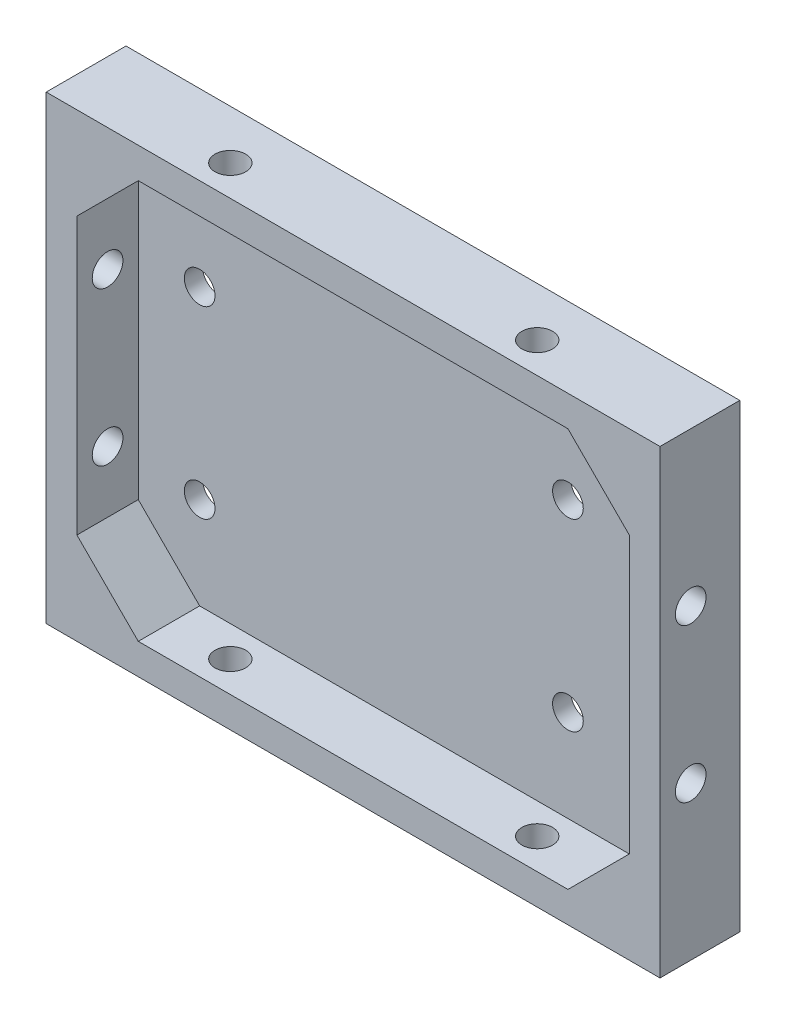
SolidWorks part; units mm, degrees
ref_plane "Plan de face" through (0, 0, 0) normal (0, 0, 1) x (1, 0, 0)
ref_plane "Plan de dessus" through (0, 0, 0) normal (0, 1, 0) x (1, 0, 0)
ref_plane "Plan de droite" through (0, 0, 0) normal (1, 0, 0) x (0, 0, -1)
sketch "Esquisse1" plane through (0, 0, 0) normal (0, 0, 1) x (1, 0, 0)
  line L0 (44.1184, 33.7284) -> (54.1184, 33.7284)
  line L1 (-45.8816, 33.7284) -> (44.1184, 33.7284)
  line L2 (-45.8816, 33.7284) -> (-45.8816, -41.2716)
  line L3 (-45.8816, -41.2716) -> (54.1184, -41.2716)
  line L4 (54.1184, 23.7284) -> (54.1184, -41.2716)
  line L5 (54.1184, 33.7284) -> (54.1184, 23.7284)
  point P6 (54.1184, 33.7284)
  dimension "D1" = 100
  dimension "D2" = 75
extrude "Boss.-Extru.1" add sketch "Esquisse1" along normal blind 13
shell "Coque1" thickness 5
sketch "Esquisse2" plane through (-45.8816, 0, 0) normal (-1, 0, 0) x (0, 0, 1)
  line L0 (13, 33.7284) -> (13, -41.2716) construction
  line L1 (13, 33.7284) -> (0, 33.7284) construction
  line L2 (13, -41.2716) -> (0, -41.2716) construction
  circle A0 centre (8, 8.7284) radius 2.5
  circle A1 centre (8, -16.2716) radius 2.5
  dimension "D1" = 5
  dimension "D2" = 5
  dimension "D3" = 5
  dimension "D4" = 5
  dimension "D5" = 25
  dimension "D6" = 25
extrude "Enlèv. mat.-Extru.1" cut sketch "Esquisse2" against normal up to surface (100 mm away) contours A1 | A0 up to face at (54.1184, -3.7716, 6.5)
sketch "Esquisse3" plane through (0, -41.2716, 0) normal (0, -1, 0) x (1, 0, 0)
  line L0 (-45.8816, 13) -> (54.1184, 13) construction
  line L2 (54.1184, 13) -> (54.1184, 0) construction
  line L3 (-45.8816, 13) -> (-45.8816, 0) construction
  circle A0 centre (-20.8816, 8) radius 2.5
  circle A1 centre (29.1184, 8) radius 2.5
  dimension "D1" = 5
  dimension "D2" = 5
  dimension "D3" = 5
  dimension "D4" = 5
  dimension "D5" = 25
  dimension "D6" = 25
extrude "Enlèv. mat.-Extru.2" cut sketch "Esquisse3" against normal up to surface (75 mm away) up to face at (4.1184, 33.7284, 6.5)
sketch "Esquisse4" plane through (0, 0, 3) normal (0, 0, 1) x (1, 0, 0)
  line L0 (-30.8816, 28.7284) -> (-40.8816, 18.7284)
  line L1 (49.1184, 28.7284) -> (-40.8816, 28.7284) construction
  line L2 (-40.8816, 28.7284) -> (-40.8816, -36.2716) construction
  line L3 (-40.8816, 18.7284) -> (-40.8816, 28.7284)
  line L4 (-40.8816, 28.7284) -> (-30.8816, 28.7284)
  line L5 (49.1184, 28.7284) -> (49.1184, 18.7284)
  line L6 (49.1184, -36.2716) -> (49.1184, 28.7284) construction
  line L7 (49.1184, 18.7284) -> (39.1184, 28.7284)
  line L8 (39.1184, 28.7284) -> (49.1184, 28.7284)
  line L9 (49.1184, 28.7284) -> (-40.8816, 28.7284) construction
  line L10 (49.1184, -36.2716) -> (49.1184, -26.2716)
  line L11 (49.1184, -26.2716) -> (39.1184, -36.2716)
  line L12 (-40.8816, -36.2716) -> (49.1184, -36.2716) construction
  line L13 (39.1184, -36.2716) -> (49.1184, -36.2716)
  line L14 (-30.8816, -36.2716) -> (-40.8816, -26.2716)
  line L15 (-40.8816, 28.7284) -> (-40.8816, -36.2716) construction
  line L16 (-40.8816, -26.2716) -> (-40.8816, -36.2716)
  line L17 (-40.8816, -36.2716) -> (-30.8816, -36.2716)
  dimension "D1" = 10
  dimension "D2" = 10
  dimension "D3" = 10
  dimension "D4" = 10
  dimension "D5" = 10
  dimension "D6" = 10
  dimension "D7" = 10
  dimension "D8" = 10
extrude "Boss.-Extru.2" add sketch "Esquisse4" along normal up to surface (10 mm away) up to face at (4.1184, -3.7716, 13)
sketch "Esquisse6" plane through (0, 0, 3) normal (0, 0, 1) x (1, 0, 0)
  line L0 (-45.8816, -41.2716) -> (54.1184, -41.2716) construction
  line L1 (54.1184, -41.2716) -> (54.1184, 33.7284) construction
  line L3 (-45.8816, 33.7284) -> (-45.8816, -41.2716) construction
  line L4 (54.1184, 33.7284) -> (-45.8816, 33.7284) construction
  circle A0 centre (-30.8816, -21.2716) radius 2.5
  circle A1 centre (29.1184, -21.2716) radius 2.5
  circle A2 centre (-30.8816, 8.7284) radius 2.5
  circle A3 centre (29.1184, 8.7284) radius 2.5
  circle A4 centre (39.1184, 19.6056) radius 5
  dimension "D2" = 5
  dimension "D3" = 5
  dimension "D4" = 15
  dimension "D6" = 20
  dimension "D8" = 15
  dimension "D9" = 10
  dimension "D7" = 5
  dimension "D12" = 5
  dimension "D5" = 20
  dimension "D10" = 25
  dimension "D11" = 25
  dimension "D13" = 25
  dimension "D14" = 25
  dimension "D15" = 15
extrude "Enlèv. mat.-Extru.3" cut sketch "Esquisse6" against normal up to surface (3 mm away) up to face at (4.1184, -3.7716, 0)
